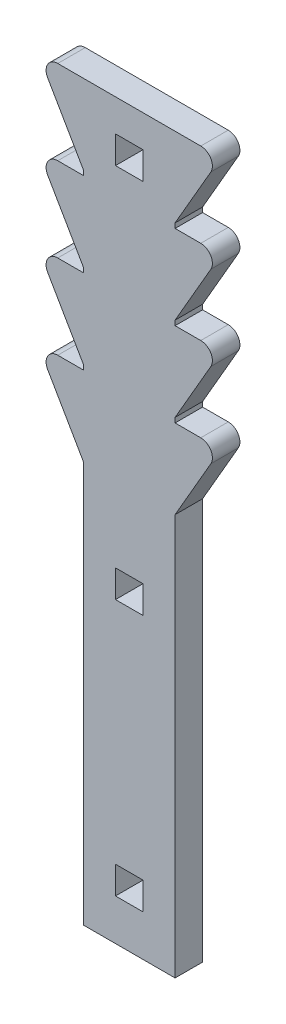
SolidWorks part; units mm, degrees
ref_plane "Alzado" through (0, 0, 0) normal (0, 0, 1) x (1, 0, 0)
ref_plane "Planta" through (0, 0, 0) normal (0, 1, 0) x (1, 0, 0)
ref_plane "Vista lateral" through (0, 0, 0) normal (1, 0, 0) x (0, 0, -1)
sketch "Sketch2" plane through (0, 0, 0) normal (0, 0, 1) x (1, 0, 0)
  line L0 (75, 273.0953) -> (75, 200) construction
  line L2 (75, 0) -> (75, -200)
  line L3 (75, -200) -> (25, -200)
  line L4 (25, 0) -> (25, -200)
  line L5 (25, 273.0953) -> (25, 200) construction
  line L6 (125, 0) -> (75, 0) construction
  line L7 (75, 110.7606) -> (100, 154.0619)
  line L8 (75, 156.6987) -> (100, 200)
  line L9 (100, 200) -> (0, 200)
  line L10 (0, 200) -> (25, 156.6987)
  line L11 (100, 154.0619) -> (75, 154.0619)
  line L12 (0, 154.0619) -> (25, 110.7606)
  line L13 (75, 64.8224) -> (100, 108.1237)
  line L14 (100, 108.1237) -> (75, 108.1237)
  line L15 (0, 108.1237) -> (25, 64.8224)
  line L16 (75, 18.8843) -> (100, 62.1856)
  line L17 (100, 62.1856) -> (75, 62.1856)
  line L18 (0, 62.1856) -> (25, 18.8843)
  line L19 (25, 154.0619) -> (0, 154.0619)
  line L20 (25, 108.1237) -> (0, 108.1237)
  line L22 (75, 0) -> (75, 18.8843)
  line L24 (25, 156.6987) -> (25, 154.0619)
  line L25 (75, 62.1856) -> (75, 64.8224)
  line L26 (75, 108.1237) -> (75, 110.7606)
  line L27 (75, 154.0619) -> (75, 156.6987)
  line L28 (25, 110.7606) -> (25, 108.1237)
  line L29 (25, 64.8224) -> (25, 62.1856)
  line L30 (25, 62.1856) -> (0, 62.1856)
  line L31 (25, 18.8843) -> (25, 0)
  line L32 (42.5, -177.5) -> (57.5, -177.5)
  line L33 (42.5, -177.5) -> (42.5, -162.5)
  line L34 (42.5, -162.5) -> (57.5, -162.5)
  line L35 (57.5, -177.5) -> (57.5, -162.5)
  line L36 (42.5, -177.5) -> (57.5, -162.5) construction
  line L37 (42.5, -162.5) -> (57.5, -177.5) construction
  line L38 (42.5, -37.5) -> (57.5, -37.5)
  line L39 (42.5, -37.5) -> (42.5, -22.5)
  line L40 (42.5, -22.5) -> (57.5, -22.5)
  line L41 (57.5, -37.5) -> (57.5, -22.5)
  line L42 (42.5, -37.5) -> (57.5, -22.5) construction
  line L43 (42.5, -22.5) -> (57.5, -37.5) construction
  line L44 (42.5, 167.5) -> (57.5, 167.5)
  line L45 (42.5, 167.5) -> (42.5, 182.5)
  line L46 (42.5, 182.5) -> (57.5, 182.5)
  line L47 (57.5, 167.5) -> (57.5, 182.5)
  line L48 (42.5, 167.5) -> (57.5, 182.5) construction
  line L49 (42.5, 182.5) -> (57.5, 167.5) construction
  point P9 (50, -170)
  point P10 (50, -30)
  point P27 (50, 175)
  point P48 (50, -200)
  dimension "D1" = 200
  dimension "D2" = 100
  dimension "D3" = 4
  dimension "D4" = 200
  dimension "D5" = 25
  dimension "D6" = 25
  dimension "D7" = 45.9381
  dimension "D8" = 15
  dimension "D9" = 30
  dimension "D10" = 30
  dimension "D11" = 25
extrude "Boss-Extrude1" add sketch "Sketch2" against normal blind 15
fillet "Fillet1" radius 6.35 8 edges at (0, 62.1856, -7.5) (0, 108.1237, -7.5) (0, 154.0619, -7.5) (0, 200, -7.5) (100, 62.1856, -7.5) (100, 108.1237, -7.5) (100, 154.0619, -7.5) (100, 200, -7.5)
